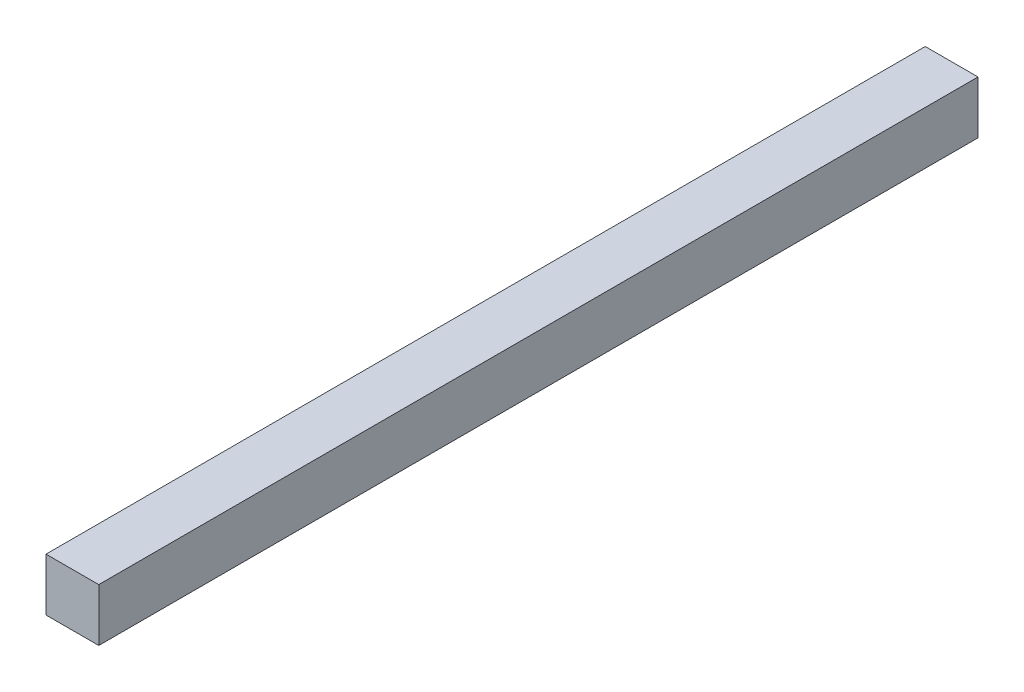
SolidWorks part; units mm, degrees
material "Balsa"
ref_plane "Front Plane" through (0, 0, 0) normal (0, 0, 1) x (1, 0, 0)
ref_plane "Top Plane" through (0, 0, 0) normal (0, 1, 0) x (1, 0, 0)
ref_plane "Right Plane" through (0, 0, 0) normal (1, 0, 0) x (0, 0, -1)
sketch "Sketch1" plane through (0, 0, 0) normal (0, 0, 1) x (1, 0, 0)
  line L1 (-15, -15) -> (15, -15)
  line L2 (-15, -15) -> (-15, 15)
  line L3 (-15, 15) -> (15, 15)
  line L4 (15, -15) -> (15, 15)
  line L5 (-15, -15) -> (15, 15) construction
  line L6 (-15, 15) -> (15, -15) construction
  point P0 (0, 0)
  dimension "D1" = 30
  dimension "D2" = 30
extrude "Boss-Extrude1" add sketch "Sketch1" along normal blind 500
